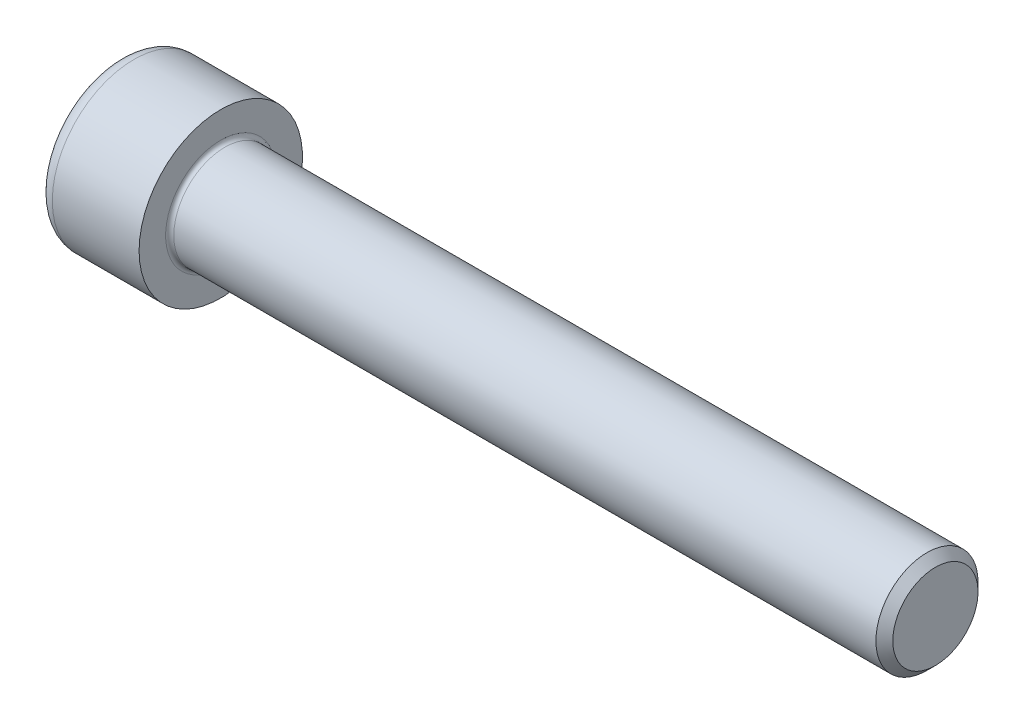
SolidWorks part; units mm, degrees
ref_plane "Plane1" through (0, 0, 0) normal (0, 0, 1) x (1, 0, 0)
ref_plane "Plane2" through (0, 0, 0) normal (0, 1, 0) x (1, 0, 0)
ref_plane "Plane3" through (0, 0, 0) normal (1, 0, 0) x (0, 0, -1)
sketch "BodySke" plane through (0, 0, 0) normal (0, 0, 1) x (1, 0, 0)
  line L0 (0, 0) -> (0, 8)
  line L1 (0, 8) -> (10, 8)
  line L2 (10, 8) -> (10, 5)
  line L3 (10, 5) -> (79.172, 5)
  line L4 (80, 4.172) -> (80, 0)
  line L5 (80, 0) -> (0, 0)
  line L6 (-31.75, 0) -> (127, 0) construction
  line L8 (80, 4.172) -> (79.172, 5)
  line L10 (80, -4.172) -> (79.172, -5) construction
  line L11 (11.5, 9.525) -> (11.5, 3.175) construction
  line L12 (20, 9.525) -> (20, 3.175) construction
  line L13 (20, 9.525) -> (20, 3.175) construction
  dimension "Diameter" = 10
  dimension "Head_ht" = 10
  dimension "Length" = 70
  dimension "Body_ch_ang" = 45
  dimension "Head_dia" = 16
  dimension "Minor_dia" = 8.344
  dimension "Advance" = 1.5
  dimension "Thread_nom" = 60
  dimension "Thread_length" = 60
revolve "Base-Revolve" add sketch "BodySke"
cosmetic thread "ThreadCosmetic" [suppressed]
fillet "Fillet1" radius 0.4 1 edges at (10, 0, 5)
fillet "Fillet2" radius 1.5 1 edges at (0, 0, 8)
sketch "Sketch2" plane through (0, 0, 0) normal (0, 0, 1) x (1, 0, 0)
  line L0 (0, 4.0575) -> (5, 4.0575)
  line L1 (5, 4.0575) -> (7.3426, 0)
  line L2 (-31.75, 0) -> (127, 0) construction
  line L3 (7.3426, 0) -> (0, 0)
  line L4 (0, 0) -> (0, 4.0575)
  line L6 (0, 0) -> (47.625, 0) construction
  dimension "D1" = 4.0575
  dimension "D2" = 60
  dimension "Depth" = 5
revolve "Hex-PreBroach" cut sketch "Sketch2" angle 360 about L6
sketch "Sketch3" plane through (0, 0, 0) normal (-1, 0, 0) x (0, 0.5, 0.866)
  line L0 (2.3426, 4.0575) -> (-2.3426, 4.0575)
  line L1 (-2.3426, 4.0575) -> (-4.6852, 0)
  line L2 (2.3426, 4.0575) -> (4.6852, 0)
  line L3 (2.3426, -4.0575) -> (4.6852, 0)
  line L4 (2.3426, -4.0575) -> (-2.3426, -4.0575)
  line L5 (-2.3426, -4.0575) -> (-4.6852, 0)
  dimension "D1" = 4.0575
  dimension "D2" = 4.0575
  dimension "Hex_size" = 8.115
extrude "Hex" cut sketch "Sketch3" against normal blind 5
sketch "ThdSchSke" plane through (0, 0, 0) normal (0, 0, 1) x (1, 0, 0)
  line L0 (20, -4.172) -> (19.4202, -5)
  line L1 (20, -4.172) -> (20.5798, -5)
  line L2 (20.5798, -5) -> (20.5798, -6.25)
  line L3 (-3.175, 0) -> (5.1513, 0) construction
  line L4 (0, 6.5) -> (0, -6.5) construction
  line L5 (20.5798, -6.25) -> (19.4202, -6.25)
  line L6 (19.4202, -6.25) -> (19.4202, -5)
  dimension "Thread_minor" = 8.344
  dimension "Diameter" = 10
  dimension "Start" = 20
  dimension "SideAngle" = 55
  dimension "VeeAngle" = 70
  dimension "Overcut" = 12.5
revolve "ThreadSchematic" [suppressed] cut sketch "ThdSchSke" angle 360 about L3
pattern_linear "ThdSchPat" [suppressed]
equation "\"D2@Sketch3\" = \"Hex_size@Sketch3\" / 2"
equation "\"D1@Sketch3\" = \"Hex_size@Sketch3\" / 2"
equation "\"D1@Sketch2\" = \"Hex_size@Sketch3\" / 2"
equation "\"Thread_minor@ThreadCosmetic\"  =  \"Minor_dia@BodySke\""
equation "\"Depth@Sketch2\" =  \"Key_eng@Hex\""
equation "\"Thread_length@ThreadCosmetic\" = ((sgn( (\"Length@BodySke\" - \"Advance@BodySke\" * 3.0) - \"Thread_nom@BodySke\" )-1)*( (\"Length@BodySke\" - \"Advance@BodySke\" * 3.0) - \"Thread_nom@BodySke\" ))/-2+ \"Thread_nom@BodySke\""
equation "\"Thread_minor@ThdSchSke\" = \"Minor_dia@BodySke\""
equation "\"Diameter@ThdSchSke\" = \"Diameter@BodySke\""
equation "\"Overcut@ThdSchSke\" = \"Diameter@BodySke\" * 1.25"
equation "\"Start@ThdSchSke\" = \"Head_ht@BodySke\" + \"Length@BodySke\" - \"Thread_length@ThreadCosmetic\"  '---Non-countersunk---"
equation "\"Num_threads@ThdSchPat\" = int( \"Thread_length@ThreadCosmetic\" / \"Advance@BodySke\" + 0.999 )  + 1"
equation "\"Advance@ThdSchPat\" = \"Thread_length@ThreadCosmetic\" /  (\"Num_threads@ThdSchPat\" - 1) 'relax it"
equation "\"Num_threads@ThdSchPat\" = \"Num_threads@ThdSchPat\" - sgn( \"Num_threads@ThdSchPat\" - 1) '---chamfered tips only---"
